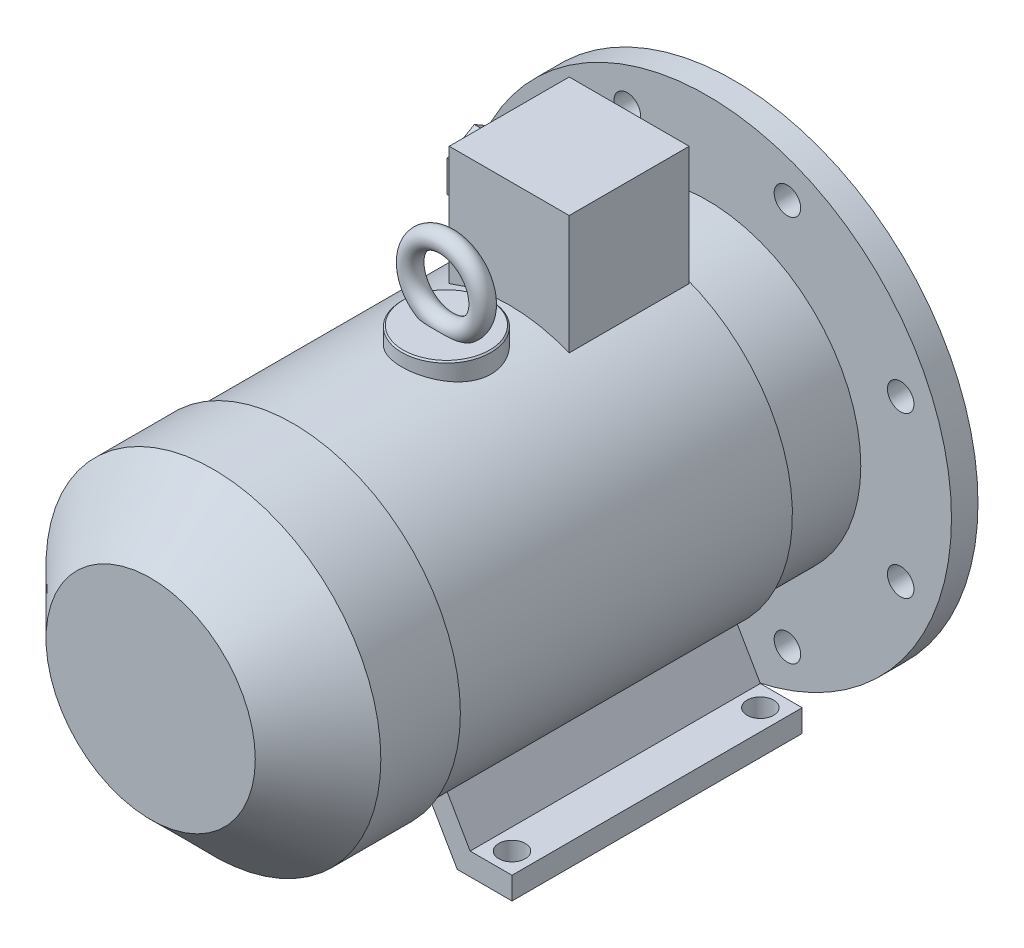
SolidWorks part; units mm, degrees
material "Ст.3 ГОСТ 380-88"
ref_plane "Спереди" through (0, 0, 0) normal (0, 0, 1) x (1, 0, 0)
ref_plane "Сверху" through (0, 0, 0) normal (0, 1, 0) x (1, 0, 0)
ref_plane "Справа" through (0, 0, 0) normal (1, 0, 0) x (0, 0, -1)
sketch "Эскиз1" plane through (0, 0, 0) normal (0, 0, 1) x (1, 0, 0)
  circle A0 centre (0, 0) radius 19
  dimension "D1" = 38
extrude "Вытянуть1" add sketch "Эскиз1" along normal blind 80
sketch "Эскиз2" plane through (0, 0, 0) normal (0, 0, -1) x (-1, 0, 0)
  line L0 (0, 0) -> (0, 21.1595) construction
  line L2 (-4, 22) -> (4, 22)
  line L3 (-4, 22) -> (-4, 14)
  line L4 (-4, 14) -> (4, 14)
  line L5 (4, 22) -> (4, 14)
  circle A1 centre (0, 0) radius 19 construction
  dimension "D1" = 8
  dimension "D2" = 8
  dimension "D3" = 41
extrude "Вытянуть2" add sketch "Эскиз2" against normal blind 60 and the other way blind 0.1
sketch "Эскиз3" plane through (0, 0, 80) normal (0, 0, 1) x (1, 0, 0)
  circle A0 centre (0, 0) radius 175
  dimension "D1" = 350
extrude "Вытянуть3" add sketch "Эскиз3" along normal blind 19
sketch "Эскиз4" plane through (0, 0, 80) normal (0, 0, -1) x (-1, 0, 0)
  circle A0 centre (0, 0) radius 125
  circle A1 centre (0, 0) radius 118
  dimension "D1" = 250
  dimension "D2" = 236
extrude "Вытянуть4" add sketch "Эскиз4" along normal blind 5
sketch "Эскиз5" plane through (0, 0, 80) normal (0, 0, -1) x (-1, 0, 0)
  circle A0 centre (0, 0) radius 118
  circle A1 centre (0, 0) radius 40
  dimension "D1" = 236
  dimension "D2" = 80
extrude "Вырез-Вытянуть1" cut sketch "Эскиз5" against normal blind 10
chamfer "Фаска1" distance 1 angle 45 3 edges at (-125, 0, 75) (-40, 0, 80) (0, -19, 0)
sketch "Эскиз6" plane through (0, 0, 80) normal (0, 0, -1) x (-1, 0, 0)
  line L0 (0, 0) -> (0, 202.3205) construction
  line L1 (0, 0) -> (-81.1873, 196.0036) construction
  circle A0 centre (-57.4025, 138.5819) radius 9.5
  circle A2 centre (57.4025, 138.5819) radius 9.5
  circle A3 centre (138.5819, 57.4025) radius 9.5
  circle A4 centre (138.5819, -57.4025) radius 9.5
  circle A5 centre (57.4025, -138.5819) radius 9.5
  circle A6 centre (-57.4025, -138.5819) radius 9.5
  circle A7 centre (-138.5819, -57.4025) radius 9.5
  circle A8 centre (-138.5819, 57.4025) radius 9.5
  dimension "D2" = 19
  dimension "D1" = 22.5
  dimension "D3" = 150
  dimension "D4" = 150
  dimension "D5" = 150
extrude "Вырез-Вытянуть2" cut sketch "Эскиз6" against normal through all
sketch "Эскиз7" plane through (0, 0, 99) normal (0, 0, 1) x (1, 0, 0)
  circle A0 centre (0, 0) radius 110
  dimension "D1" = 220
extrude "Вытянуть5" add sketch "Эскиз7" along normal blind 55
sketch "Эскиз8" plane through (0, 0, 154) normal (0, 0, 1) x (1, 0, 0)
  circle A0 centre (0, 0) radius 116
  dimension "D1" = 232
extrude "Вытянуть6" add sketch "Эскиз8" along normal blind 242
sketch "Эскиз9" plane through (0, 0, 396) normal (0, 0, 1) x (1, 0, 0)
  circle A0 centre (0, 0) radius 120
  dimension "D1" = 240
extrude "Вытянуть7" add sketch "Эскиз9" along normal blind 102
chamfer "Фаска2" distance 45 angle 45 1 edges at (120, 0, 498)
sketch "Эскиз10" plane through (0, 0, 154) normal (0, 0, -1) x (-1, 0, 0)
  line L0 (0, 0) -> (0, -210.5574) construction
  line L1 (-123, -132) -> (-83.7624, -132)
  line L2 (-83.7624, -132) -> (-58.1641, -87.6625)
  line L3 (-58.1641, -87.6625) -> (-72.0205, -79.6625)
  line L4 (-72.0205, -79.6625) -> (-93, -116)
  line L5 (-93, -116) -> (-123, -116)
  line L6 (-123, -116) -> (-123, -132)
  line L7 (123, -132) -> (83.7624, -132)
  line L8 (123, -116) -> (123, -132)
  line L9 (93, -116) -> (123, -116)
  line L10 (72.0205, -79.6625) -> (93, -116)
  line L11 (83.7624, -132) -> (58.1641, -87.6625)
  line L12 (58.1641, -87.6625) -> (72.0205, -79.6625)
  dimension "D1" = 16
  dimension "D2" = 16
  dimension "D3" = 30
  dimension "D4" = 123
  dimension "D5" = 30
  dimension "D6" = 132
  dimension "D7" = 105
extrude "Вытянуть8" add sketch "Эскиз10" against normal blind 208
sketch "Эскиз11" plane through (0, -132, 0) normal (0, -1, 0) x (1, 0, 0)
  line L0 (-174.4977, 169) -> (166.5055, 169) construction
  line L1 (0, 0) -> (0, 472.826) construction
  line L2 (-108, 169) -> (108, 169) construction
  line L3 (-108, 169) -> (-108, 347) construction
  circle A0 centre (-108, 169) radius 9.5
  circle A1 centre (108, 169) radius 9.5
  circle A2 centre (-108, 347) radius 9.5
  circle A3 centre (108, 347) radius 9.5
  dimension "D2" = 19
  dimension "D1" = 169
  dimension "D3" = 108
  dimension "D4" = 90
  dimension "D5" = 347
  dimension "D6" = 216
  dimension "D7" = 178
extrude "Вырез-Вытянуть3" cut sketch "Эскиз11" against normal up to next
sketch "Эскиз12" plane through (0, 0, 0) normal (0, 1, 0) x (1, 0, 0)
  line L0 (0, 0) -> (0, -376.9188) construction
  line L2 (-43, -155) -> (43, -155)
  line L3 (-43, -155) -> (-43, -241)
  line L4 (-43, -241) -> (43, -241)
  line L5 (43, -155) -> (43, -241)
  line L6 (116, -154) -> (-116, -154) construction
  dimension "D1" = 1
  dimension "D2" = 86
  dimension "D3" = 86
extrude "Вытянуть9" add sketch "Эскиз12" along normal blind 193
sketch "Эскиз13" plane through (0, 0, 0) normal (0, 1, 0) x (1, 0, 0)
  line L1 (0, 0) -> (0, -423.7429) construction
  circle A0 centre (0, -286) radius 32
  dimension "D1" = 64
  dimension "D2" = 286
extrude "Вытянуть10" add sketch "Эскиз13" along normal blind 126
chamfer "Фаска3" distance 1 angle 45 1 edges at (0, 126, 318)
ref_plane "Плоскость1" through (0, 0, 286) normal (0, 0, 1) x (1, 0, 0)
sketch "Эскиз14" plane through (0, 0, 286) normal (0, 0, 1) x (1, 0, 0)
  line L0 (0, 0) -> (0, 246.1233) construction
  line L1 (31, 126) -> (-31, 126) construction
  circle A0 centre (0, 152) radius 26
  dimension "D1" = 52
sketch "Эскиз15" plane through (0, 0, 0) normal (1, 0, 0) x (0, 0, -1)
  line L0 (-286, 178) -> (-286, 126) construction
  line L1 (-255, 126) -> (-317, 126) construction
  circle A0 centre (-286, 178) radius 7
  dimension "D1" = 14
  dimension "D2" = 52
sweep "По траектории1" add profiles "Эскиз15" path "Эскиз14"
sketch "Эскиз16" plane through (-43, 0, 0) normal (-1, 0, 0) x (0, 0, 1)
  line L0 (155, 193) -> (241, 193) construction
  line L1 (155, 193) -> (155, 107.7358) construction
  circle A0 centre (198, 150) radius 15
  dimension "D1" = 30
  dimension "D2" = 43
  dimension "D3" = 43
extrude "Вытянуть11" add sketch "Эскиз16" along normal blind 10
sketch "Эскиз17" plane through (-53, 0, 0) normal (-1, 0, 0) x (0, 0, 1)
  line L0 (198, 150) -> (198, 197.1554) construction
  line L1 (198, 172.5167) -> (178.5, 161.2583)
  line L2 (178.5, 161.2583) -> (178.5, 138.7417)
  line L3 (178.5, 138.7417) -> (198, 127.4833)
  line L4 (198, 127.4833) -> (217.5, 138.7417)
  line L5 (217.5, 138.7417) -> (217.5, 161.2583)
  line L6 (217.5, 161.2583) -> (198, 172.5167)
  circle A0 centre (198, 150) radius 19.5 construction
  circle A1 centre (198, 150) radius 15 construction
  dimension "D1" = 39
extrude "Вытянуть12" add sketch "Эскиз17" along normal blind 15
sketch "Эскиз18" plane through (-68, 0, 0) normal (-1, 0, 0) x (0, 0, 1)
  circle A0 centre (198, 150) radius 8
  circle A1 centre (198, 150) radius 15 construction
  dimension "D1" = 16
extrude "Вырез-Вытянуть4" cut sketch "Эскиз18" against normal blind 15
